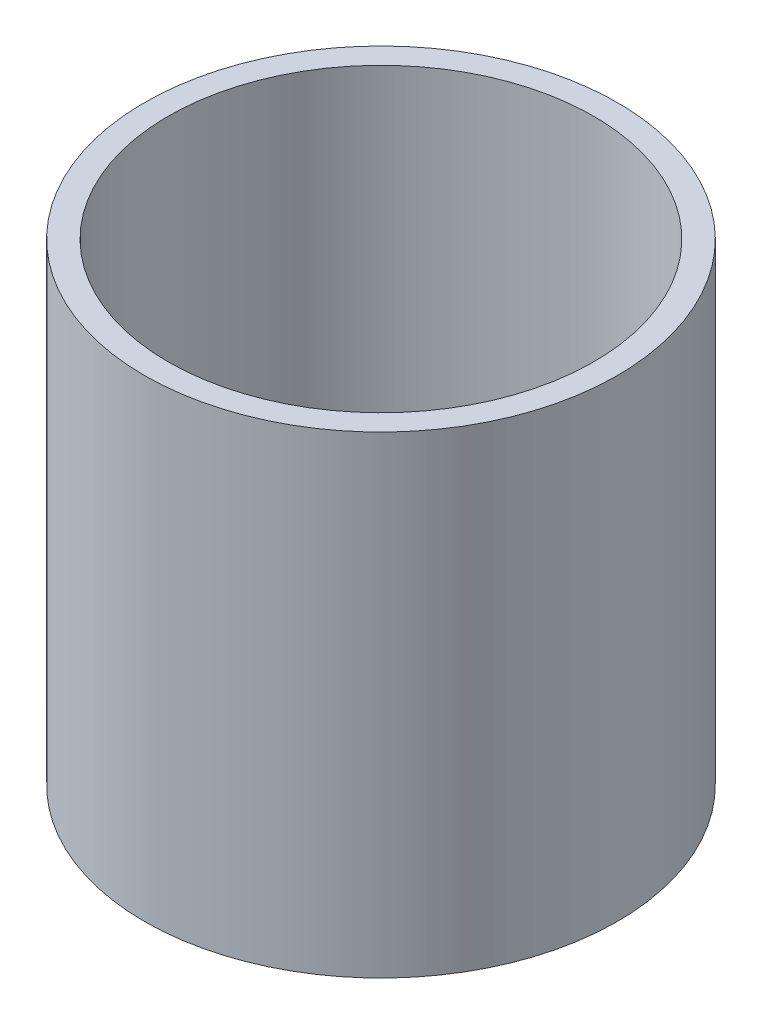
SolidWorks part; units mm, degrees
ref_plane "Plano frontal" through (0, 0, 0) normal (0, 0, 1) x (1, 0, 0)
ref_plane "Plano superior" through (0, 0, 0) normal (0, 1, 0) x (1, 0, 0)
ref_plane "Plano direito" through (0, 0, 0) normal (1, 0, 0) x (0, 0, -1)
sketch "Esboço1" plane through (0, 0, 0) normal (0, 1, 0) x (1, 0, 0)
  circle A0 centre (0, 0) radius 45
  circle A1 centre (0, 0) radius 50
  dimension "D1" = 90
  dimension "D2" = 100
extrude "Ressalto-extrusão2" add sketch "Esboço1" along normal blind 100
